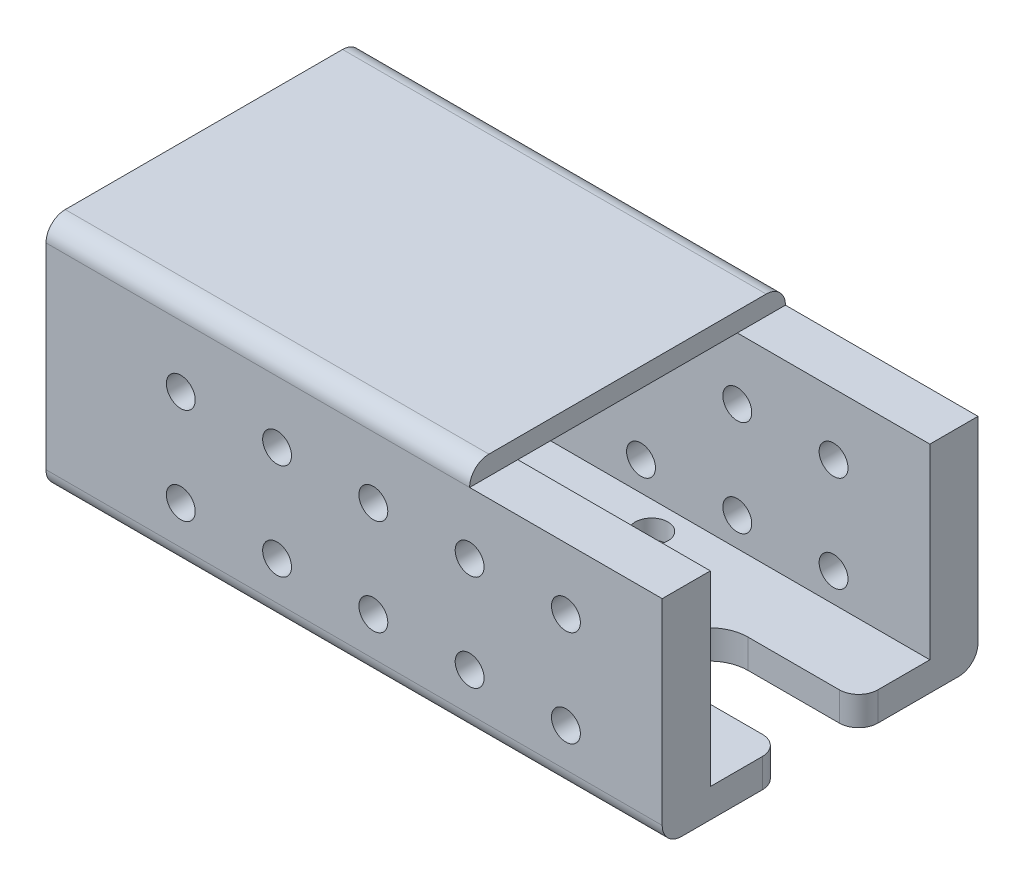
SolidWorks part; units mm, degrees
ref_plane "Plan de face" through (0, 0, 0) normal (0, 0, 1) x (1, 0, 0)
ref_plane "Plan de dessus" through (0, 0, 0) normal (0, 1, 0) x (1, 0, 0)
ref_plane "Plan de droite" through (0, 0, 0) normal (1, 0, 0) x (0, 0, -1)
sketch "Esquisse1" plane through (0, 0, 0) normal (0, 1, 0) x (1, 0, 0)
  line L1 (-30, -11.4) -> (30, -11.4)
  line L2 (-30, -11.4) -> (-30, 11.4)
  line L3 (-30, 11.4) -> (30, 11.4)
  line L4 (30, -11.4) -> (30, 11.4)
  line L5 (-30, -11.4) -> (30, 11.4) construction
  line L6 (-30, 11.4) -> (30, -11.4) construction
  point P0 (0, 0)
  dimension "D1" = 22.8
  dimension "D2" = 60
extrude "Boss.-Extru.1" add sketch "Esquisse1" along normal mid plane 3
sketch "Esquisse2" plane through (0, -1.5, 0) normal (0, -1, 0) x (1, 0, 0)
  line L0 (30, 11.4) -> (30, -11.4) construction
  line L1 (-30, -2.5) -> (30, -2.5)
  line L2 (-30, -2.5) -> (-30, 2.5)
  line L3 (-30, 2.5) -> (30, 2.5)
  line L4 (30, -2.5) -> (30, 2.5)
  line L5 (-30, -2.5) -> (30, 2.5) construction
  line L6 (-30, 2.5) -> (30, -2.5) construction
  point P0 (0, 0)
  dimension "D1" = 5
extrude "Boss.-Extru.2" add sketch "Esquisse2" along normal blind 10
sketch "Esquisse7" plane through (0, 0, -11.4) normal (0, 0, -1) x (-1, 0, 0)
  line L0 (30, -11.5) -> (30, -1.5) construction
  line L1 (-30, -1.5) -> (30, -1.5)
  line L2 (-30, -1.5) -> (-30, 20.9)
  line L3 (-30, 20.9) -> (30, 20.9)
  line L4 (30, -1.5) -> (30, 20.9)
  dimension "D1" = 22.4
extrude "Boss.-Extru.3" add sketch "Esquisse7" along normal blind 5
hole_wizard "Diamètre du perçage Ø3.0 (3)2" positions "Esquisse8" profile "Esquisse9" hole size "Ø3.0" standard "ISO"
sketch "Esquisse8" plane through (0, 0, -16.4) normal (0, 0, -1) x (-1, 0, 0)
  line L0 (-30, -1.5) -> (30, -1.5) construction
  point P0 (-20, 4.5)
  point P19 (-10, 4.5)
  point P20 (0, 4.5)
  point P21 (10, 4.5)
  point P22 (20, 4.5)
  dimension "D1" = 20
  dimension "D2" = 6
  dimension "D3" = 5
sketch "Esquisse9" plane through (20, 4.5, -16.4) normal (1, 0, 0) x (0, 1, 0)
  line L0 (0, 0) -> (0, 13.9013)
  line L1 (0, 13.9013) -> (1.5, 13)
  line L2 (1.5, 13) -> (1.5, 0)
  line L5 (1.5, 0) -> (0, 0)
  line L10 (0, 13.9013) -> (-1.5, 13) construction
  line L11 (0, -6.35) -> (0, 107.95) construction
  dimension "Diamètre du perçage" = 3
  dimension "Profondeur du perçage" = 13
  dimension "Angle de pointe" = 118
pattern_linear "Répétition linéaire2" count 2 spacing 10 along (0, 1, 0) of "Diamètre du perçage Ø3.0 (3)2"
mirror "Symétrie1" about plane through (0, 0, 0) normal (0, 0, 1) of "Répétition linéaire2", "Boss.-Extru.3", "Diamètre du perçage Ø3.0 (3)2"
hole_wizard "Diamètre du perçage Ø3.0 (3)1" positions "Esquisse3" profile "Esquisse4" hole size "Ø3.0" standard "ISO"
sketch "Esquisse3" plane through (0, 0, 2.5) normal (0, 0, 1) x (1, 0, 0)
  line L2 (30, -1.5) -> (-30, -1.5) construction
  line L3 (-30, -11.5) -> (-30, -1.5) construction
  point P4 (-20, -6.5)
  dimension "D1" = 5
  dimension "D2" = 10
sketch "Esquisse4" plane through (-20, -6.5, 2.5) normal (1, 0, 0) x (0, -1, 0)
  line L0 (0, 0) -> (0, 13.9013)
  line L1 (0, 13.9013) -> (1.5, 13)
  line L2 (1.5, 13) -> (1.5, 0)
  line L5 (1.5, 0) -> (0, 0)
  line L10 (0, 13.9013) -> (-1.5, 13) construction
  line L11 (0, -6.35) -> (0, 107.95) construction
  dimension "Diamètre du perçage" = 3
  dimension "Profondeur du perçage" = 13
  dimension "Angle de pointe" = 118
hole_wizard "Chambrage pour vis à six pans creux M31" positions "Esquisse5" profile "Esquisse6" counterbore size "M3" standard "ISO"
sketch "Esquisse5" plane through (0, -1.5, 0) normal (0, -1, 0) x (-1, 0, 0)
  point P0 (-4, 8.5)
  point P3 (-4, -8.5)
sketch "Esquisse6" plane through (4, -1.5, -8.5) normal (1, 0, 0) x (0, 0, -1)
  line L0 (0, 0) -> (0, 14.0215)
  line L1 (0, 14.0215) -> (1.7, 13)
  line L2 (1.7, 13) -> (1.7, 1)
  line L3 (1.7, 1) -> (3.25, 1)
  line L4 (3.25, 1) -> (3.25, 0)
  line L5 (3.25, 0) -> (0, 0)
  line L10 (0, 14.0215) -> (-1.7, 13) construction
  line L11 (0, -6.35) -> (0, 107.95) construction
  dimension "Diamètre du perçage" = 3.4
  dimension "Profondeur du perçage" = 13
  dimension "Diamètre du chambrage" = 6.5
  dimension "Profondeur du chambrage" = 1
  dimension "Angle de pointe" = 118
pattern_linear "Répétition linéaire1" count 3 spacing 10 along (1, 0, 0) of "Diamètre du perçage Ø3.0 (3)1"
sketch "Esquisse10" plane through (0, 20.9, 0) normal (0, 1, 0) x (1, 0, 0)
  line L0 (-30, -16.4) -> (30, -16.4) construction
  line L1 (-30, 16.4) -> (10, 16.4)
  line L2 (-30, 16.4) -> (-30, -16.4)
  line L3 (-30, -16.4) -> (10, -16.4)
  line L4 (10, 16.4) -> (10, -16.4)
  dimension "D1" = 40
extrude "Boss.-Extru.4" add sketch "Esquisse10" along normal blind 2
sketch "Esquisse11" plane through (0, 0, 0) normal (0, 0, 1) x (1, 0, 0)
  line L1 (30, -11.5) -> (10, -11.5)
  line L2 (30, -11.5) -> (30, -1.5)
  line L3 (30, -1.5) -> (10, -1.5)
  line L4 (10, -11.5) -> (10, -1.5)
  line L6 (30, -1.5) -> (-30, -1.5) construction
  point P5 (0, 0)
  point P6 (15, -1.5)
  point P7 (0, 0)
  point P8 (0, 0)
  point P9 (10, -1.5)
  point P10 (0, 0)
  dimension "D1" = 20
extrude "Enlèv. mat.-Extru.1" cut sketch "Esquisse11" against normal through all both and the other way through all
sketch "Esquisse12" plane through (0, 0, 0) normal (0, 1, 0) x (1, 0, 0)
  line L0 (30, -16.4) -> (30, 16.4) construction
  line L1 (18.5, 4) -> (30, 4)
  line L2 (18.5, 4) -> (18.5, -4)
  line L3 (18.5, -4) -> (30, -4)
  line L4 (30, 4) -> (30, -4)
  circle A0 centre (18.5, 0) radius 4
  dimension "D1" = 8
  dimension "D2" = 8
extrude "Enlèv. mat.-Extru.2" cut sketch "Esquisse12" against normal through all both and the other way through all contours L1 L4 L3 L2 | A0
sketch "Esquisse13" plane through (-30, 0, 0) normal (-1, 0, 0) x (0, 0, 1)
  line L0 (16.4, -1.5) -> (16.4, 22.9) construction
  line L1 (-16.4, 22.9) -> (16.4, 22.9)
  line L2 (-16.4, 22.9) -> (-16.4, 8.9)
  line L3 (-16.4, 8.9) -> (16.4, 8.9)
  line L4 (16.4, 22.9) -> (16.4, 8.9)
  line L5 (-16.4, 8.9) -> (-16.4, -1.5)
  line L6 (-16.4, -1.5) -> (-2.5, -1.5)
  line L7 (-2.5, -1.5) -> (-2.5, -11.5)
  line L8 (-2.5, -11.5) -> (2.5, -11.5)
  line L9 (2.5, -11.5) -> (2.5, -1.5)
  line L10 (2.5, -1.5) -> (16.4, -1.5)
  line L11 (16.4, -1.5) -> (16.4, 8.9)
  line L12 (11.3597, 8.9) -> (11.4, 1.5)
  line L13 (11.4, 1.5) -> (-11.4, 1.5)
  line L14 (-11.4, 1.5) -> (-11.4, 8.9)
  line L15 (-11.4, 1.5) -> (-11.4, 20.9) construction
  line L16 (-11.4, 8.9) -> (-16.4, 8.9)
  line M2 (-11.4, 1.5) -> (-11.4, 20.9)
  line M3 (-11.4, 20.9) -> (11.4, 20.9)
  line M4 (11.4, 20.9) -> (11.4, 1.5)
  line M5 (11.4, 1.5) -> (-11.4, 1.5)
  line M6 (-16.4, -1.5) -> (-2.5, -1.5)
  line M7 (-2.5, -1.5) -> (-2.5, -11.5)
  line M8 (-2.5, -11.5) -> (2.5, -11.5)
  line M9 (2.5, -11.5) -> (2.5, -1.5)
  line M10 (2.5, -1.5) -> (16.4, -1.5)
  line M11 (16.4, -1.5) -> (16.4, 22.9)
  line M12 (16.4, 22.9) -> (-16.4, 22.9)
  line M13 (-16.4, 22.9) -> (-16.4, -1.5)
  dimension "D1" = 14
extrude "Boss.-Extru.5" add sketch "Esquisse13" along normal blind 4 contours L3 M13 M2 M3 M4 M11 M12 | L3 M2 M4 M3 | L3 M13 M6 M7 M8 M9 M10 M11 M4 M5 M2
sketch "Esquisse14" plane through (-34, 0, 0) normal (-1, 0, 0) x (0, 0, 1)
  line L0 (0, -18.92) -> (0, 18.92) construction
  line L5 (6, 20.0106) -> (8, 20.0106)
  line L6 (6, 20.0106) -> (6, 12.0106)
  line L7 (6, 12.0106) -> (8, 12.0106)
  line L8 (8, 20.0106) -> (8, 12.0106)
  line L9 (-6, 12.0106) -> (-8, 12.0106)
  line L10 (-8, 20.0106) -> (-8, 12.0106)
  line L11 (-6, 20.0106) -> (-8, 20.0106)
  line L12 (-6, 20.0106) -> (-6, 12.0106)
  point P11 (0, 0)
  point P12 (0, 0)
  point P13 (0, 0)
  point P14 (0, 0)
  point P15 (0, 0)
  point P16 (0, 0)
  point P17 (0, 0)
  dimension "D1" = 8
  dimension "D2" = 2
  dimension "D3" = 6
extrude "Enlèv. mat.-Extru.3" cut sketch "Esquisse14" against normal through all both and the other way through all
fillet "Congé2" radius 2 11 edges at (-12, -1.5, -2.5) (10, 21.9, 16.4) (10, 21.9, -16.4) (-12, 22.9, 16.4) (-12, 22.9, -16.4) (-12, -1.5, 2.5) (10, -1.5, 0) (30, 0, -4) (30, 0, 4) (-2, -1.5, -16.4) (-2, -1.5, 16.4)
sketch "Esquisse15" plane through (-30, 0, 0) normal (-1, 0, 0) x (0, 0, 1)
  line L1 (-7.4, 1.5) -> (7.4, 1.5)
  line L2 (-7.4, 1.5) -> (-7.4, 0)
  line L3 (-7.4, 0) -> (7.4, 0)
  line L4 (7.4, 1.5) -> (7.4, 0)
  line L6 (-11.4, 1.5) -> (-11.4, 8.9) construction
  line L7 (11.4, 8.9) -> (11.4, 1.5) construction
  point P5 (0, 0)
  point P8 (0, 0)
  point P9 (0, 0)
  point P10 (0, 0)
  point P12 (0, 0)
  point P13 (0, 0)
  dimension "D1" = 1.5
  dimension "D2" = 4
  dimension "D3" = 4
extrude "Enlèv. mat.-Extru.4" cut sketch "Esquisse15" against normal blind 25 and the other way through all
fillet "Congé3" radius 0.5 6 edges at (-19.5, 0, -7.4) (-5, 0, 0) (-19.5, 0, 7.4) (-5, 1.5, 0) (-19.5, 1.5, -7.4) (-19.5, 1.5, 7.4)
